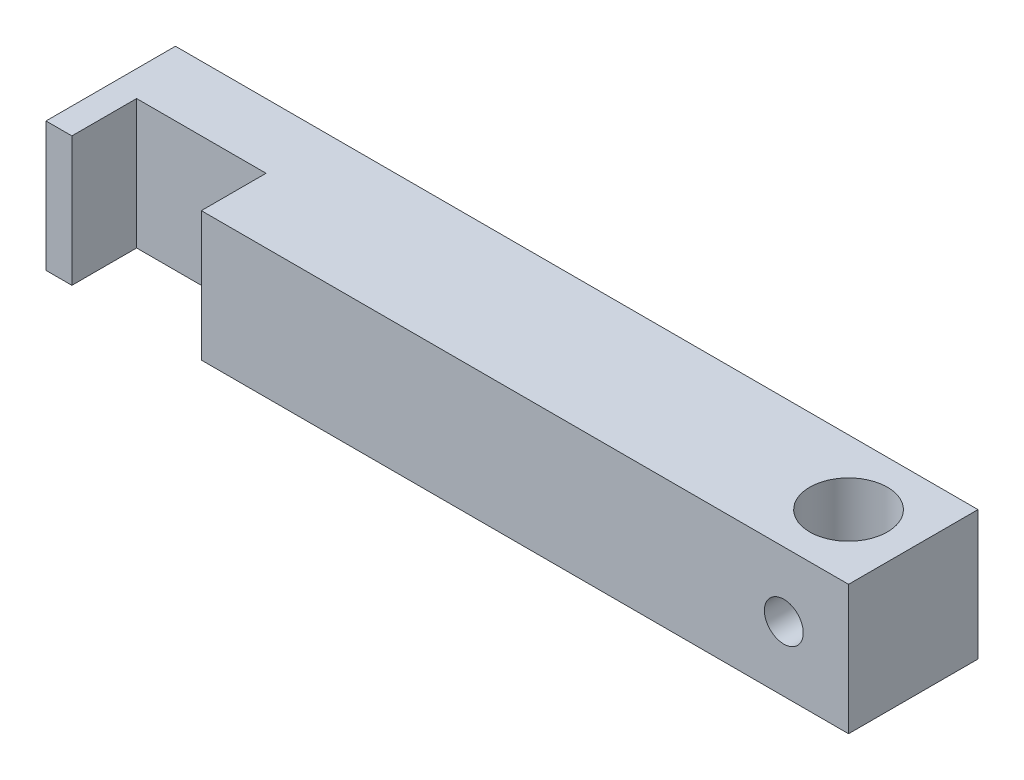
SolidWorks part; units mm, degrees
ref_plane "前基準面" through (0, 0, 0) normal (0, 0, 1) x (1, 0, 0)
ref_plane "上基準面" through (0, 0, 0) normal (0, 1, 0) x (1, 0, 0)
ref_plane "右基準面" through (0, 0, 0) normal (1, 0, 0) x (0, 0, -1)
sketch "草圖1" plane through (0, 0, 0) normal (0, 1, 0) x (1, 0, 0)
  line L0 (-55, -5) -> (-55, 0)
  line L1 (-57, 5) -> (5, 5)
  line L2 (-57, 5) -> (-57, -5)
  line L3 (-57, -5) -> (-55, -5)
  line L4 (5, 5) -> (5, -5)
  line L5 (-55, 0) -> (-45, 0)
  line L6 (-45, 0) -> (-45, -5)
  line L7 (-45, -5) -> (5, -5)
  circle A0 centre (0, 0) radius 3
  point P8 (5, 0)
  dimension "D1" = 5
  dimension "hole" = 6
  dimension "D2" = 10
  dimension "length" = 62
  dimension "D4" = 5
  dimension "D5" = 10
  dimension "D6" = 2
extrude "填料-伸長1" add sketch "草圖1" along normal mid plane 10
sketch "草圖3" plane through (0, 0, 5) normal (0, 0, 1) x (1, 0, 0)
  circle A0 centre (0, 0) radius 1.5
  dimension "D1" = 3
extrude "除料-伸長1" cut sketch "草圖3" against normal through all
